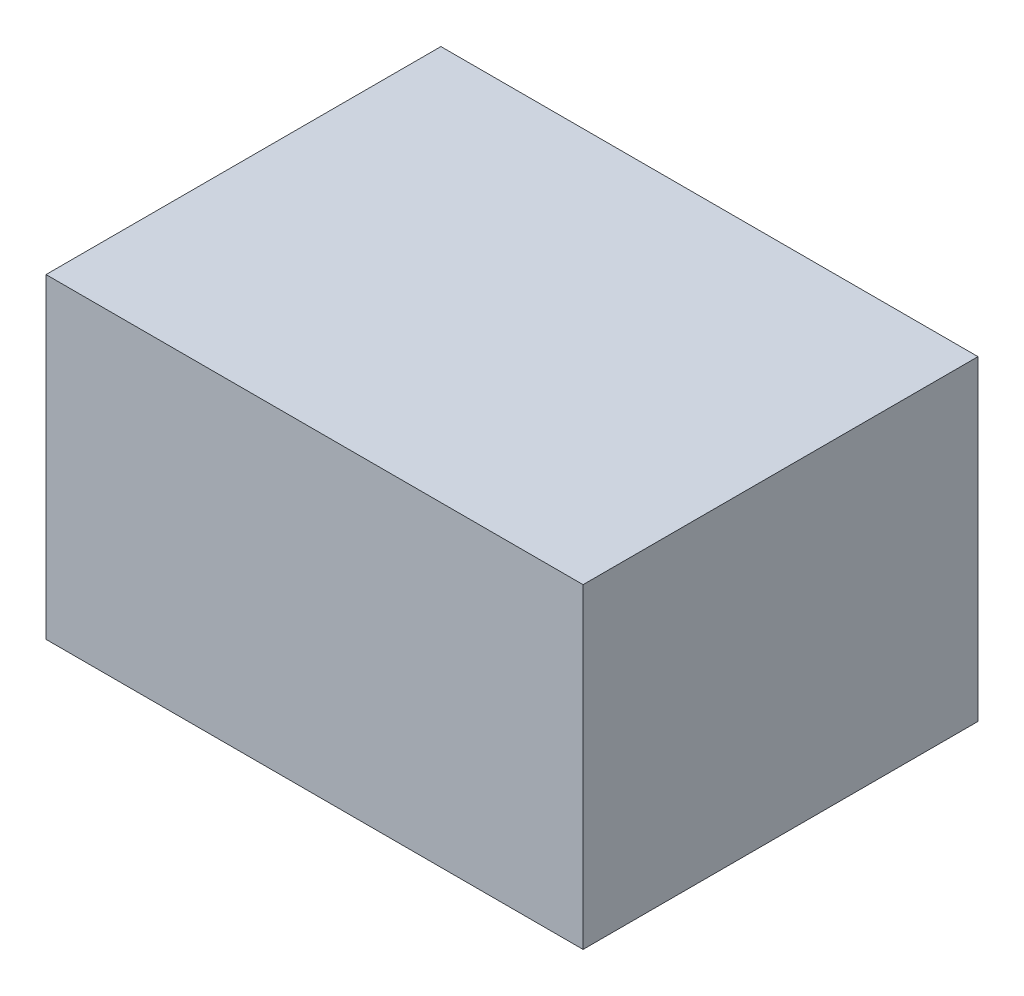
SolidWorks part; units mm, degrees
ref_plane "Front Plane" through (0, 0, 0) normal (0, 0, 1) x (1, 0, 0)
ref_plane "Top Plane" through (0, 0, 0) normal (0, 1, 0) x (1, 0, 0)
ref_plane "Right Plane" through (0, 0, 0) normal (1, 0, 0) x (0, 0, -1)
sketch "Sketch1" plane through (0, 0, 0) normal (0, 1, 0) x (1, 0, 0)
  line L1 (0, 0) -> (340, 0)
  line L2 (0, 0) -> (0, 250)
  line L3 (0, 250) -> (340, 250)
  line L4 (340, 0) -> (340, 250)
  dimension "D1" = 250
  dimension "D2" = 340
extrude "Boss-Extrude1" add sketch "Sketch1" along normal blind 200
